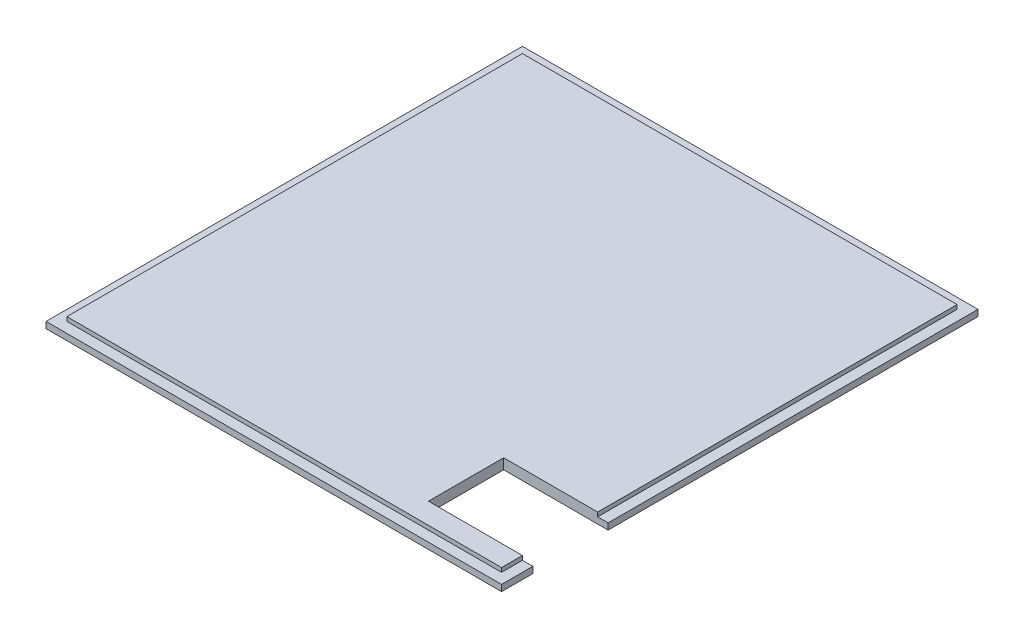
SolidWorks part; units mm, degrees
ref_plane "Front Plane" through (0, 0, 0) normal (0, 0, 1) x (1, 0, 0)
ref_plane "Top Plane" through (0, 0, 0) normal (0, 1, 0) x (1, 0, 0)
ref_plane "Right Plane" through (0, 0, 0) normal (1, 0, 0) x (0, 0, -1)
sketch "Sketch2" plane through (0, 0, 0) normal (0, 1, 0) x (1, 0, 0)
  line L1 (54.5, -57) -> (-54.5, -57)
  line L2 (54.5, -57) -> (54.5, 57)
  line L3 (54.5, 57) -> (-54.5, 57)
  line L4 (-54.5, -57) -> (-54.5, 57)
  line L5 (54.5, -57) -> (-54.5, 57) construction
  line L6 (54.5, 57) -> (-54.5, -57) construction
  point P0 (0, 0)
  dimension "D1" = 109
  dimension "D2" = 114
extrude "Boss-Extrude1" add sketch "Sketch2" along normal blind 1.5
sketch "Sketch3" plane through (0, 1.5, 0) normal (0, 1, 0) x (1, 0, 0)
  line L1 (52, -54.5) -> (-52, -54.5)
  line L2 (52, -54.5) -> (52, 54.5)
  line L3 (52, 54.5) -> (-52, 54.5)
  line L4 (-52, -54.5) -> (-52, 54.5)
  line L5 (52, -54.5) -> (-52, 54.5) construction
  line L6 (52, 54.5) -> (-52, -54.5) construction
  point P0 (0, 0)
  dimension "D1" = 109
  dimension "D2" = 104
extrude "Boss-Extrude2" add sketch "Sketch3" along normal blind 1
sketch "Sketch4" plane through (0, 2.5, 0) normal (0, 1, 0) x (1, 0, 0)
  line L0 (54.5, -57) -> (54.5, 57) construction
  line L1 (54.5, -49.5) -> (29.5, -49.5)
  line L2 (54.5, -49.5) -> (54.5, -31.5)
  line L3 (54.5, -31.5) -> (29.5, -31.5)
  line L4 (29.5, -49.5) -> (29.5, -31.5)
  line L5 (-52, -54.5) -> (52, -54.5) construction
  dimension "D1" = 18
  dimension "D2" = 25
  dimension "D3" = 5
extrude "Cut-Extrude1" cut sketch "Sketch4" against normal up to surface (2.5 mm away) up to face at (0, 0, 0)
